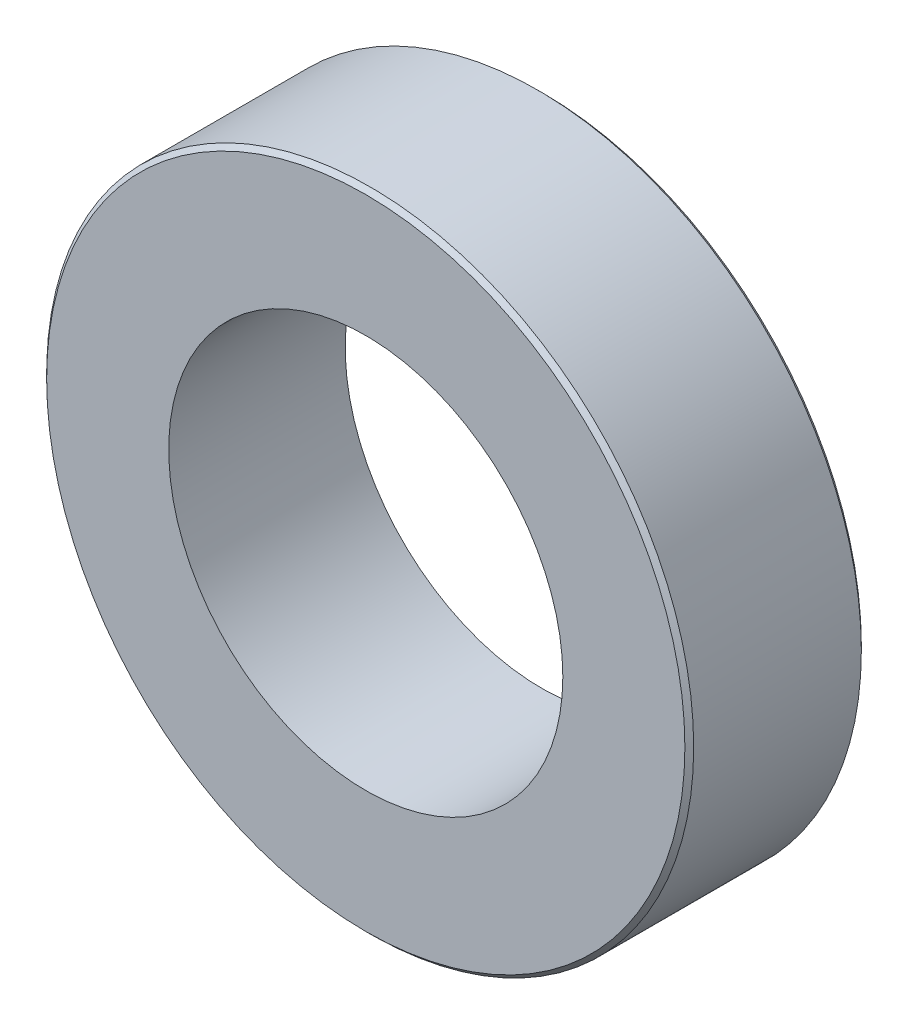
SolidWorks part; units mm, degrees
material "Cast Alloy Steel"
ref_plane "Front Plane" through (0, 0, 0) normal (0, 0, 1) x (1, 0, 0)
ref_plane "Top Plane" through (0, 0, 0) normal (0, 1, 0) x (1, 0, 0)
ref_plane "Right Plane" through (0, 0, 0) normal (1, 0, 0) x (0, 0, -1)
sketch "Sketch1" plane through (0, 0, 0) normal (0, 0, 1) x (1, 0, 0)
  circle A0 centre (0, 0) radius 11
  circle A1 centre (0, 0) radius 6.7
  dimension "D1" = 22
  dimension "D2" = 4.3
extrude "Boss-Extrude1" add sketch "Sketch1" along normal mid plane 6
chamfer "Chamfer1" distance 0.15 angle 45 2 edges at (11, 0, -3) (11, 0, 3)
